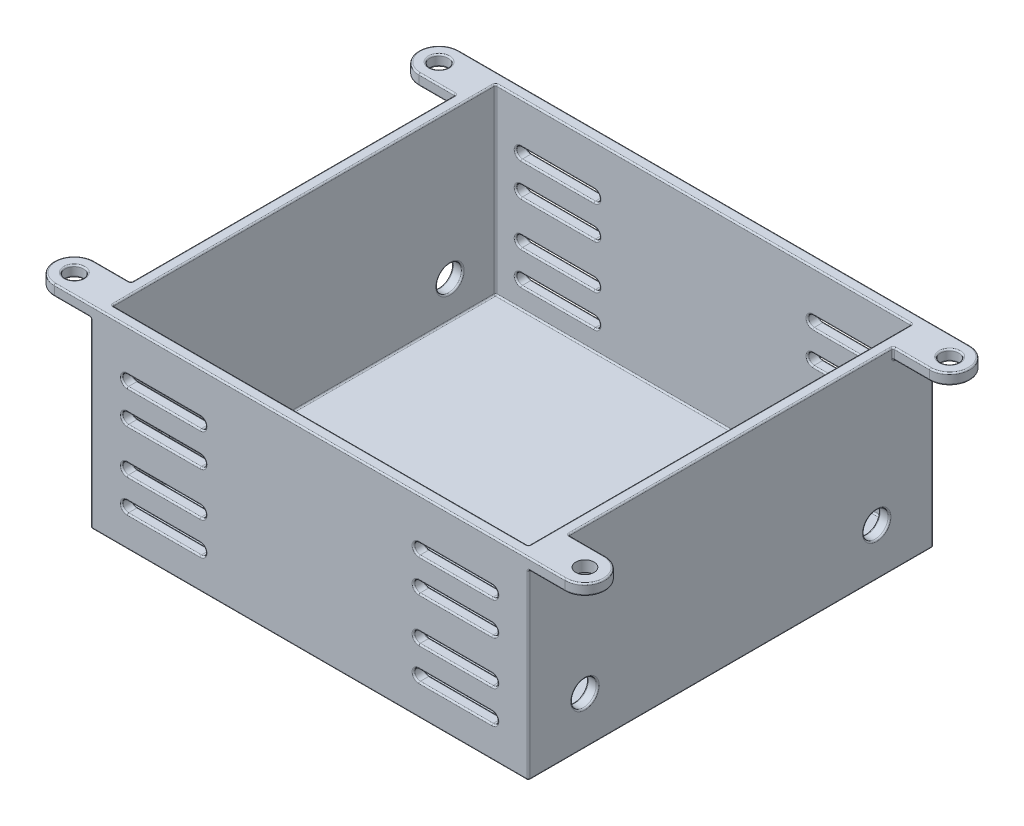
SolidWorks part; units mm, degrees
ref_plane "Front Plane" through (0, 0, 0) normal (0, 0, 1) x (1, 0, 0)
ref_plane "Top Plane" through (0, 0, 0) normal (0, 1, 0) x (1, 0, 0)
ref_plane "Right Plane" through (0, 0, 0) normal (1, 0, 0) x (0, 0, -1)
sketch "Sketch1" plane through (0, 0, 0) normal (0, 1, 0) x (1, 0, 0)
  line L0 (-35, 27.75) -> (35, 27.75) construction
  line L1 (35, 25) -> (-35, 25) construction
  line L2 (35, 25) -> (35, -25) construction
  line L3 (35, -25) -> (-35, -25) construction
  line L4 (-35, 25) -> (-35, -25) construction
  line L5 (35, 25) -> (-35, -25) construction
  line L6 (35, -25) -> (-35, 25) construction
  line L7 (-30, 27.75) -> (-30, -27.75)
  line L8 (-35, -27.75) -> (34.9994, -27.75) construction
  line L9 (-30, -27.75) -> (30, -27.75)
  line L10 (30, -27.75) -> (30, 27.75)
  line L11 (30, 27.75) -> (-30, 27.75)
  line L12 (-35, 22.25) -> (-30, 22.25)
  line L13 (-35, -22.25) -> (-30, -22.25)
  line L14 (35, 22.25) -> (29.9996, 22.25)
  line L15 (35, -22.25) -> (30, -22.25)
  line L16 (28.5, 26.25) -> (-28.5, 26.25)
  line L17 (-28.5, 26.25) -> (-28.5, -26.25)
  line L18 (-28.5, -26.25) -> (28.5, -26.25)
  line L19 (28.5, -26.25) -> (28.5, 26.25)
  circle A0 centre (-35, 25) radius 1.25
  circle A1 centre (35, 25) radius 1.25
  circle A2 centre (35, -25) radius 1.25
  circle A3 centre (-35, -25) radius 1.25
  circle A4 centre (-35, 25) radius 2.75
  circle A5 centre (35, 25) radius 2.75
  circle A6 centre (35, -25) radius 2.75
  circle A7 centre (-35, -25) radius 2.75
  point P0 (0, 0)
  point P30 (0, 27.75)
  dimension "D3" = 2.5
  dimension "D1" = 70
  dimension "D2" = 50
  dimension "D5" = 60
  dimension "D4" = 1.5
  dimension "D6" = 1.5
extrude "Boss-Extrude1" add sketch "Sketch1" against normal blind 25 contours L10 L11 L7 L9 L19 L18 L17 L16
sketch "Sketch2" plane through (0, -25, 0) normal (0, -1, 0) x (1, 0, 0)
  line L4 (30, -27.75) -> (30, 27.75)
  line L5 (30, 27.75) -> (-30, 27.75)
  line L6 (-30, 27.75) -> (-30, -27.75)
  line L7 (-30, -27.75) -> (30, -27.75)
  line L8 (30, -27.75) -> (30, 27.75)
  line L9 (30, 27.75) -> (-30, 27.75)
  line L10 (-30, 27.75) -> (-30, -27.75)
  line L11 (-30, -27.75) -> (30, -27.75)
  dimension "D1" = 0
extrude "Boss-Extrude2" add sketch "Sketch2" along normal blind 1.5
sketch "Sketch4" plane through (0, 0, 0) normal (0, 1, 0) x (1, 0, 0)
  line L0 (35, 22.25) -> (29.9996, 22.25) construction
  line L1 (-35, -22.25) -> (-30, -22.25) construction
  line L2 (-35, 22.25) -> (-30, 22.25) construction
  line L3 (35, -22.25) -> (30, -22.25) construction
  line L4 (-30, 27.75) -> (-30, -27.75)
  line L5 (-30, -27.75) -> (30, -27.75)
  line L6 (30, -27.75) -> (30, 27.75)
  line L7 (30, 27.75) -> (-30, 27.75)
  line L8 (-30, 27.75) -> (-30, 22.25)
  line L10 (30, -27.75) -> (30, -22.25)
  line L20 (35, 22.25) -> (29.9996, 22.25)
  line L21 (-35, -22.25) -> (-30, -22.25)
  line L22 (-35, 22.25) -> (-30, 22.25)
  line L23 (35, -22.25) -> (30, -22.25)
  line L24 (-30, 27.75) -> (-35, 27.75)
  line L25 (35, 27.75) -> (30, 27.75)
  line L26 (35, -27.75) -> (30, -27.75)
  line L27 (-35, -27.75) -> (-30, -27.75)
  line L28 (-30, -22.25) -> (-30, -27.75)
  line L29 (30, 22.25) -> (30, 27.75)
  circle A1 centre (35, -25) radius 2.75
  circle A2 centre (35, -25) radius 2.75
  circle A3 centre (35, 25) radius 2.75
  circle A4 centre (35, 25) radius 2.75
  circle A5 centre (-35, 25) radius 2.75
  circle A6 centre (-35, 25) radius 2.75
  circle A7 centre (-35, -25) radius 1.25
  circle A8 centre (-35, -25) radius 1.25
  circle A9 centre (35, -25) radius 1.25
  circle A10 centre (35, -25) radius 1.25
  circle A11 centre (35, 25) radius 1.25
  circle A12 centre (35, 25) radius 1.25
  circle A13 centre (-35, 25) radius 1.25
  circle A14 centre (-35, 25) radius 1.25
  circle A15 centre (-35, -25) radius 2.75
  circle A16 centre (-35, -25) radius 2.75
  circle A17 centre (35, -25) radius 1.25
  point P26 (0, 0)
  line M21 (30, -27.75) -> (30, 27.75)
  line M23 (-30, 27.75) -> (-30, -27.75)
  dimension "D1" = 0
  dimension "D2" = 0
  dimension "D3" = 0
  dimension "D4" = 0
  dimension "D5" = 0
  dimension "D6" = 0
  dimension "D7" = 0
  dimension "D8" = 0
  dimension "D9" = 0
extrude "Boss-Extrude3" add sketch "Sketch4" against normal blind 1.5 contours A16 L27 L21 M23 | A6 L22 L24 M23 | A6 A14 | A16 A8 | A4 A12 | A4 L25 L20 M21 | A2 L23 L26 M21
sketch "Sketch5" plane through (0, 0, 0) normal (0, 0, 1) x (1, 0, 0)
  line L0 (-30, -14) -> (30, -14) construction
  line L1 (-30, -26.5) -> (-30, -1.5) construction
  line L2 (30, -26.5) -> (30, -1.5) construction
  line L3 (-25, -6.5) -> (-15, -6.5) construction
  line L4 (-25, -5.75) -> (-15, -5.75)
  line L5 (-25, -7.25) -> (-15, -7.25)
  line L6 (0, -14) -> (0, -21.676) construction
  line L7 (-25, -11) -> (-15, -11) construction
  line L8 (-25, -10.25) -> (-15, -10.25)
  line L9 (-25, -11.75) -> (-15, -11.75)
  line L10 (-25, -21.5) -> (-15, -21.5) construction
  line L11 (-25, -22.25) -> (-15, -22.25)
  line L12 (-25, -20.75) -> (-15, -20.75)
  line L13 (-25, -17) -> (-15, -17) construction
  line L14 (-25, -17.75) -> (-15, -17.75)
  line L15 (-25, -16.25) -> (-15, -16.25)
  line L16 (25, -6.5) -> (15, -6.5) construction
  line L17 (25, -5.75) -> (15, -5.75)
  line L18 (25, -7.25) -> (15, -7.25)
  line L19 (25, -11) -> (15, -11) construction
  line L20 (25, -10.25) -> (15, -10.25)
  line L21 (25, -11.75) -> (15, -11.75)
  line L22 (25, -21.5) -> (15, -21.5) construction
  line L23 (25, -22.25) -> (15, -22.25)
  line L24 (25, -20.75) -> (15, -20.75)
  line L25 (25, -17) -> (15, -17) construction
  line L26 (25, -17.75) -> (15, -17.75)
  line L27 (25, -16.25) -> (15, -16.25)
  arc A0 (-25, -5.75) -> (-25, -7.25) centre (-25, -6.5) ccw
  arc A1 (-15, -7.25) -> (-15, -5.75) centre (-15, -6.5) ccw
  arc A2 (-25, -10.25) -> (-25, -11.75) centre (-25, -11) ccw
  arc A3 (-15, -11.75) -> (-15, -10.25) centre (-15, -11) ccw
  arc A4 (-25, -22.25) -> (-25, -20.75) centre (-25, -21.5) cw
  arc A5 (-15, -20.75) -> (-15, -22.25) centre (-15, -21.5) cw
  arc A6 (-25, -17.75) -> (-25, -16.25) centre (-25, -17) cw
  arc A7 (-15, -16.25) -> (-15, -17.75) centre (-15, -17) cw
  arc A8 (25, -5.75) -> (25, -7.25) centre (25, -6.5) cw
  arc A9 (15, -7.25) -> (15, -5.75) centre (15, -6.5) cw
  arc A10 (25, -10.25) -> (25, -11.75) centre (25, -11) cw
  arc A11 (15, -11.75) -> (15, -10.25) centre (15, -11) cw
  arc A12 (25, -22.25) -> (25, -20.75) centre (25, -21.5) ccw
  arc A13 (15, -20.75) -> (15, -22.25) centre (15, -21.5) ccw
  arc A14 (25, -17.75) -> (25, -16.25) centre (25, -17) ccw
  arc A15 (15, -16.25) -> (15, -17.75) centre (15, -17) ccw
  point P8 (-20, -6.5)
  point P13 (-14.25, -6.5)
  point P17 (-20, -11)
  point P26 (-20, -21.5)
  point P33 (-20, -17)
  point P40 (20, -6.5)
  point P47 (20, -11)
  point P54 (20, -21.5)
  point P61 (20, -17)
  dimension "D1" = 10
  dimension "D2" = 0.75
  dimension "D3" = 7.5
  dimension "D4" = 20
  dimension "D5" = 4.5
extrude "Cut-Extrude1" cut sketch "Sketch5" against normal up to surface and the other way up to surface up to face at (0, -7.375, -27.75) other way up to face at (0, -7.375, 27.75)
sketch "Sketch7" plane through (0, 0, 0) normal (1, 0, 0) x (0, 0, -1)
  line L0 (0, 0) -> (0, -20) construction
  line L1 (0, -20) -> (-20, -20) construction
  circle A0 centre (-20, -20) radius 1.75
  circle A1 centre (20, -20) radius 1.75
  dimension "D1" = 3.5
  dimension "D2" = 20
  dimension "D3" = 20
extrude "Cut-Extrude2" cut sketch "Sketch7" along normal up to surface and the other way up to surface up to face at (30, -7.375, 0) other way up to face at (-30, -7.375, 0)
fillet "Fillet1" radius 0.2 194 edges at (30, -20, -21.75) (-30, -20, -18.25) (-30, -20, 21.75) (30, -20, 18.25) (-28.5, -20, -18.25) (28.5, -20, -21.75) (-28.5, -20, 21.75) (28.5, -20, 18.25) (25.75, -17, -27.75) (20, -17.75, -27.75) (14.25, -17, -27.75) (20, -16.25, -27.75) (14.25, -17, 27.75) (20, -16.25, 27.75) (25.75, -17, 27.75) (20, -17.75, 27.75) (25.75, -21.5, -27.75) (20, -22.25, -27.75) (14.25, -21.5, -27.75) (20, -20.75, -27.75) (14.25, -21.5, 27.75) (20, -20.75, 27.75) (25.75, -21.5, 27.75) (20, -22.25, 27.75) (25.75, -11, -27.75) (20, -11.75, -27.75) (14.25, -11, -27.75) (20, -10.25, -27.75) (14.25, -11, 27.75) (20, -10.25, 27.75) (25.75, -11, 27.75) (20, -11.75, 27.75) (25.75, -6.5, -27.75) (20, -7.25, -27.75) (14.25, -6.5, -27.75) (20, -5.75, -27.75) (14.25, -6.5, 27.75) (20, -5.75, 27.75) (25.75, -6.5, 27.75) (20, -7.25, 27.75) (-25.75, -17, -27.75) (-20, -16.25, -27.75) (-14.25, -17, -27.75) (-20, -17.75, -27.75) (-14.25, -17, 27.75) (-20, -17.75, 27.75) (-25.75, -17, 27.75) (-20, -16.25, 27.75) (-25.75, -21.5, -27.75) (-20, -20.75, -27.75) (-14.25, -21.5, -27.75) (-20, -22.25, -27.75) (-14.25, -21.5, 27.75) (-20, -22.25, 27.75) (-25.75, -21.5, 27.75) (-20, -20.75, 27.75) (-25.75, -11, -27.75) (-20, -10.25, -27.75) (-14.25, -11, -27.75) (-20, -11.75, -27.75) (-14.25, -11, 27.75) (-20, -11.75, 27.75) (-25.75, -11, 27.75) (-20, -10.25, 27.75) (-20, -5.75, 27.75) (-25.75, -6.5, 27.75) (-20, -7.25, 27.75) (-14.25, -6.5, 27.75) (-20, -7.25, -27.75) (-14.25, -6.5, -27.75) (-20, -5.75, -27.75) (-25.75, -6.5, -27.75) (-25.75, -6.5, 26.25) (-25.75, -6.5, -26.25) (-20, -5.75, 26.25) (-20, -5.75, -26.25) (-14.25, -6.5, 26.25) (-14.25, -6.5, -26.25) (-20, -7.25, 26.25) (-20, -7.25, -26.25) (25.75, -11, 26.25) (25.75, -11, -26.25) (20, -11.75, 26.25) (20, -11.75, -26.25) (14.25, -11, 26.25) (14.25, -11, -26.25) (20, -10.25, 26.25) (20, -10.25, -26.25) (25.75, -21.5, 26.25) (25.75, -21.5, -26.25) (20, -22.25, 26.25) (20, -22.25, -26.25) (14.25, -21.5, 26.25) (14.25, -21.5, -26.25) (20, -20.75, 26.25) (20, -20.75, -26.25) (25.75, -17, 26.25) (25.75, -17, -26.25) (20, -17.75, 26.25) (20, -17.75, -26.25) (14.25, -17, 26.25) (14.25, -17, -26.25) (20, -16.25, 26.25) (20, -16.25, -26.25) (-25.75, -11, 26.25) (-25.75, -11, -26.25) (-20, -10.25, 26.25) (-20, -10.25, -26.25) (-14.25, -11, 26.25) (-14.25, -11, -26.25) (-20, -11.75, 26.25) (-20, -11.75, -26.25) (-25.75, -21.5, 26.25) (-25.75, -21.5, -26.25) (-20, -20.75, 26.25) (-20, -20.75, -26.25) (-14.25, -21.5, 26.25) (-14.25, -21.5, -26.25) (-20, -22.25, 26.25) (-20, -22.25, -26.25) (-25.75, -17, 26.25) (-25.75, -17, -26.25) (-20, -16.25, 26.25) (-20, -16.25, -26.25) (-14.25, -17, 26.25) (-14.25, -17, -26.25) (-20, -17.75, 26.25) (-20, -17.75, -26.25) (25.75, -6.5, 26.25) (25.75, -6.5, -26.25) (20, -7.25, 26.25) (20, -7.25, -26.25) (14.25, -6.5, 26.25) (14.25, -6.5, -26.25) (20, -5.75, 26.25) (20, -5.75, -26.25) (30, -0.75, 22.25) (32.5, -1.5, 27.75) (30, -1.5, 25) (32.5, -1.5, 22.25) (32.5, 0, 22.25) (37.75, -1.5, 25) (37.75, 0, 25) (30, -0.75, -22.25) (32.5, 0, -22.25) (32.5, -1.5, -22.25) (30, -1.5, -25) (32.5, -1.5, -27.75) (37.75, 0, -25) (37.75, -1.5, -25) (35, -1.5, -23.75) (35, 0, -23.75) (-30, -0.75, 22.25) (-35, -1.5, 26.25) (-35, 0, 26.25) (-30, -1.5, 25) (-32.5, -1.5, 27.75) (-37.75, 0, 25) (-37.75, -1.5, 25) (-32.5, 0, 22.25) (-32.5, -1.5, 22.25) (-37.75, 0, -25) (-37.75, -1.5, -25) (-32.5, 0, -22.25) (-32.5, -1.5, -22.25) (-35, -1.5, -23.75) (-35, 0, -23.75) (-32.5, -1.5, -27.75) (-30, -1.5, -25) (-30, -0.75, -22.25) (0, -26.5, -27.75) (30, -26.5, 0) (0, -26.5, 27.75) (-30, -26.5, 0) (28.5, 0, 0) (28.5, -25, 0) (0, 0, 26.25) (0, -25, 26.25) (-28.5, 0, 0) (-28.5, -25, 0) (0, 0, -26.25) (0, -25, -26.25) (30, 0, 0) (0, 0, -27.75) (-30, 0, 0) (0, 0, 27.75) (28.5, -12.5, 26.25) (-28.5, -12.5, 26.25) (-28.5, -12.5, -26.25) (28.5, -12.5, -26.25) (-30, -14, -27.75) (-30, -14, 27.75) (30, -14, 27.75) (30, -14, -27.75)
sketch "Sketch8" plane through (0, 0, 0) normal (0, 1, 0) x (1, 0, 0)
  circle A0 centre (35, -25) radius 1.25
extrude "Cut-Extrude3" cut sketch "Sketch8" against normal blind 10
